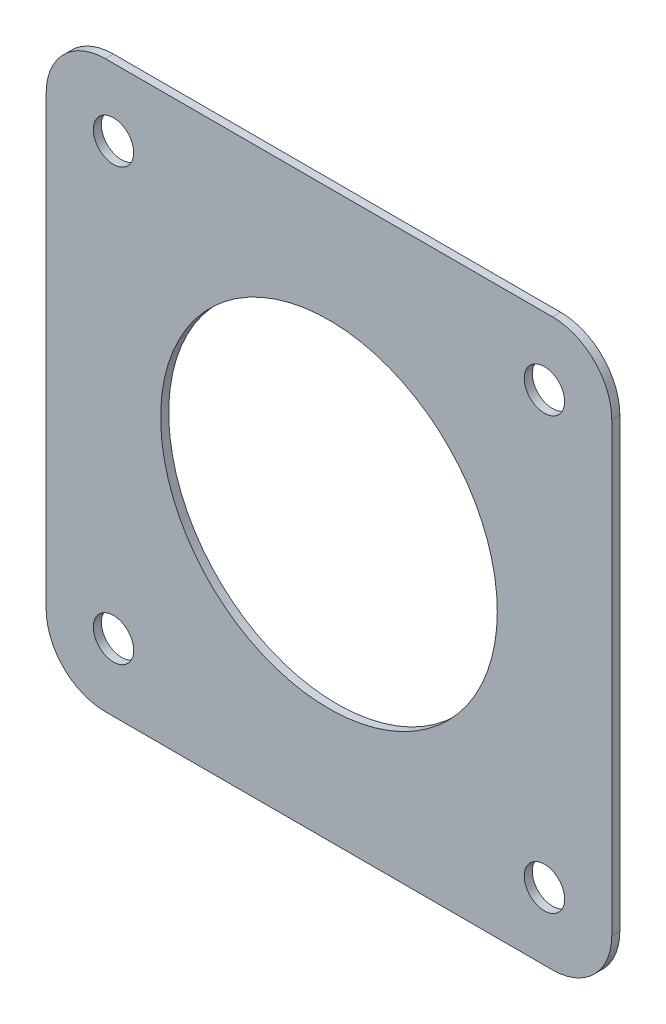
SolidWorks part; units mm, degrees
material "Резина"
ref_plane "Спереди" through (0, 0, 0) normal (0, 0, 1) x (1, 0, 0)
ref_plane "Сверху" through (0, 0, 0) normal (0, 1, 0) x (1, 0, 0)
ref_plane "Справа" through (0, 0, 0) normal (1, 0, 0) x (0, 0, -1)
sketch "Эскиз1" plane through (0, 0, 0) normal (0, 0, 1) x (1, 0, 0)
  line L4 (-83, -105) -> (83, -105)
  line L5 (105, -83) -> (105, 83)
  line L6 (83, 105) -> (-83, 105)
  line L7 (-105, 83) -> (-105, -83)
  line L8 (-83, -105) -> (83, -105)
  line L9 (105, -83) -> (105, 83)
  line L10 (83, 105) -> (-83, 105)
  line L11 (-105, 83) -> (-105, -83)
  circle A0 centre (-80, 80) radius 7.5 construction
  circle A1 centre (-80, 80) radius 7.5
  circle A2 centre (80, 80) radius 7.5 construction
  circle A3 centre (80, -80) radius 7.5 construction
  arc A4 (83, -105) -> (105, -83) centre (83, -83) ccw
  arc A5 (105, 83) -> (83, 105) centre (83, 83) ccw
  arc A6 (-83, 105) -> (-105, 83) centre (-83, 83) ccw
  arc A7 (-105, -83) -> (-83, -105) centre (-83, -83) ccw
  arc A8 (83, -105) -> (105, -83) centre (83, -83) ccw
  arc A9 (105, 83) -> (83, 105) centre (83, 83) ccw
  arc A10 (-83, 105) -> (-105, 83) centre (-83, 83) ccw
  arc A11 (-105, -83) -> (-83, -105) centre (-83, -83) ccw
  circle A12 centre (-80, -80) radius 7.5 construction
  circle A13 centre (80, 80) radius 7.5
  circle A14 centre (80, -80) radius 7.5
  circle A15 centre (-80, -80) radius 7.5
  circle A16 centre (0, 0) radius 62.5
  dimension "D2" = 125
  dimension "D1" = 0
extrude "Бобышка-Вытянуть1" add sketch "Эскиз1" along normal blind 3
